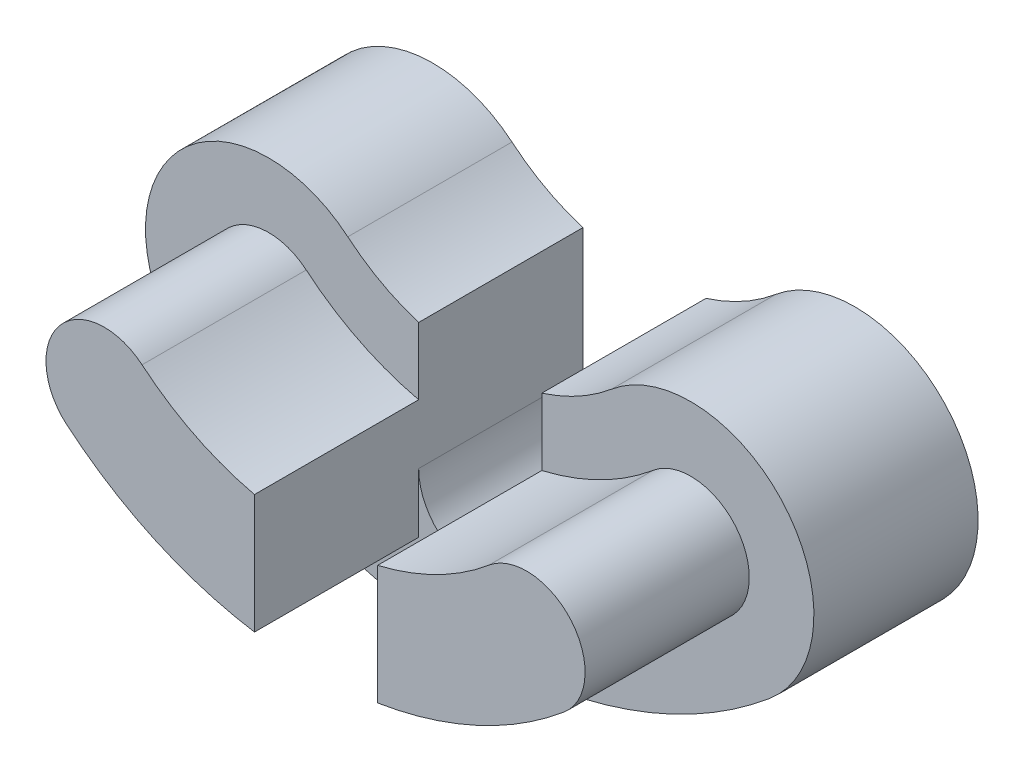
SolidWorks part; units mm, degrees
ref_plane "Front Plane" through (0, 0, 0) normal (0, 0, 1) x (1, 0, 0)
ref_plane "Top Plane" through (0, 0, 0) normal (0, 1, 0) x (1, 0, 0)
ref_plane "Right Plane" through (0, 0, 0) normal (1, 0, 0) x (0, 0, -1)
sketch "Sketch1" plane through (0, 0, 0) normal (0, 0, 1) x (1, 0, 0)
  line L0 (0, 0) -> (0, -16) construction
  line L1 (0, 0) -> (10.2846, -12.2567) construction
  line L2 (-2.9749, -12.8091) -> (-2.9749, -18.6138)
  line L3 (-2.9749, -15.7114) -> (3.0251, -15.7114) construction
  line L4 (3.0251, -12.7973) -> (3.0251, -18.6057)
  arc A0 (-10.2846, -12.2567) -> (10.2846, -12.2567) centre (0, 0) ccw construction
  arc A1 (-12.213, -14.5548) -> (12.213, -14.5548) centre (0, 0) ccw construction
  arc A2 (-8.3562, -9.9586) -> (8.3562, -9.9586) centre (0, 0) ccw construction
  arc A3 (-8.3562, -9.9586) -> (-12.213, -14.5548) centre (-10.2846, -12.2567) ccw construction
  arc A4 (12.213, -14.5548) -> (8.3562, -9.9586) centre (10.2846, -12.2567) ccw construction
  arc A5 (-12.1165, -14.4399) -> (12.1165, -14.4399) centre (0, 0) ccw
  arc A6 (12.1165, -14.4399) -> (8.4527, -10.0735) centre (10.2846, -12.2567) ccw
  arc A7 (-8.4527, -10.0735) -> (8.4527, -10.0735) centre (0, 0) ccw
  arc A8 (-8.4527, -10.0735) -> (-12.1165, -14.4399) centre (-10.2846, -12.2567) ccw
  point P4 (0, -16)
  dimension "D2" = 3
  dimension "D3" = 16
  dimension "D5" = 6
  dimension "D4" = 0.15
extrude "Boss-Extrude1" add sketch "Sketch1" along normal blind 8 contours A7 A8 A5 L2 | A7 L4 A5 A6
sketch "Sketch2" plane through (0, 0, 0) normal (0, 0, -1) x (-1, 0, 0)
  line L1 (-3.0251, -12.7973) -> (-3.0251, -9.5315)
  line L2 (-3.0251, -12.7973) -> (-3.0251, -15.7114)
  line L3 (2.9749, -15.7114) -> (2.9749, -9.5472)
  arc A0 (-10.2846, -12.2567) -> (10.2846, -12.2567) centre (0, 0) ccw construction
  arc A1 (-14.1413, -16.853) -> (14.1413, -16.853) centre (0, 0) ccw
  arc A2 (-6.4279, -7.6604) -> (6.4279, -7.6604) centre (0, 0) ccw
  arc A3 (-6.4279, -7.6604) -> (-14.1413, -16.853) centre (-10.2846, -12.2567) ccw
  arc A4 (14.1413, -16.853) -> (6.4279, -7.6604) centre (10.2846, -12.2567) ccw
  arc A6 (-10.2846, -12.2567) -> (10.2846, -12.2567) centre (0, 0) ccw construction
  arc A7 (-8.3562, -9.9586) -> (-12.213, -14.5548) centre (-10.2846, -12.2567) ccw construction
  arc A8 (-3.0251, -15.7114) -> (2.9749, -15.7114) centre (-0.0251, -15.7114) ccw
  point P4 (0, -16)
  point P18 (-3.0251, -9.5472)
  point P24 (0, 0)
  arc M5 (8.4527, -10.0735) -> (2.9749, -12.8091) centre (0, 0) cw
  line M6 (2.9749, -12.8091) -> (2.9749, -18.6138)
  arc M7 (2.9749, -18.6138) -> (12.1165, -14.4399) centre (0, 0) ccw
  arc M8 (12.1165, -14.4399) -> (8.4527, -10.0735) centre (10.2846, -12.2567) ccw
  dimension "D1" = 3
extrude "Boss-Extrude2" add sketch "Sketch2" along normal blind 8 contours A8 L2 L1 A2 A3 A1 A4 L3 M5 M8 M7 M6 | M8 M5 M6 M7
